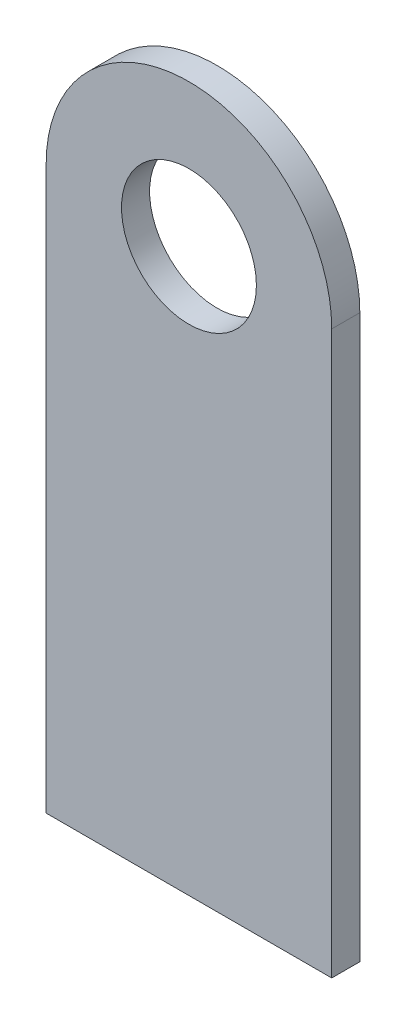
SolidWorks part; units mm, degrees
ref_plane "Front Plane" through (0, 0, 0) normal (0, 0, 1) x (1, 0, 0)
ref_plane "Top Plane" through (0, 0, 0) normal (0, 1, 0) x (1, 0, 0)
ref_plane "Right Plane" through (0, 0, 0) normal (1, 0, 0) x (0, 0, -1)
sketch "Sketch1" plane through (0, 0, 0) normal (0, 0, 1) x (1, 0, 0)
  line L0 (-12.7, 0) -> (-12.7, -50)
  line L1 (-12.7, -50) -> (12.7, -50)
  line L2 (12.7, -50) -> (12.7, 0)
  circle A0 centre (0, 0) radius 6
  arc A1 (12.7, 0) -> (-12.7, 0) centre (0, 0) ccw
  dimension "D1" = 12
  dimension "D2" = 25.4
  dimension "D3" = 50
extrude "Boss-Extrude1" add sketch "Sketch1" along normal blind 2.5
